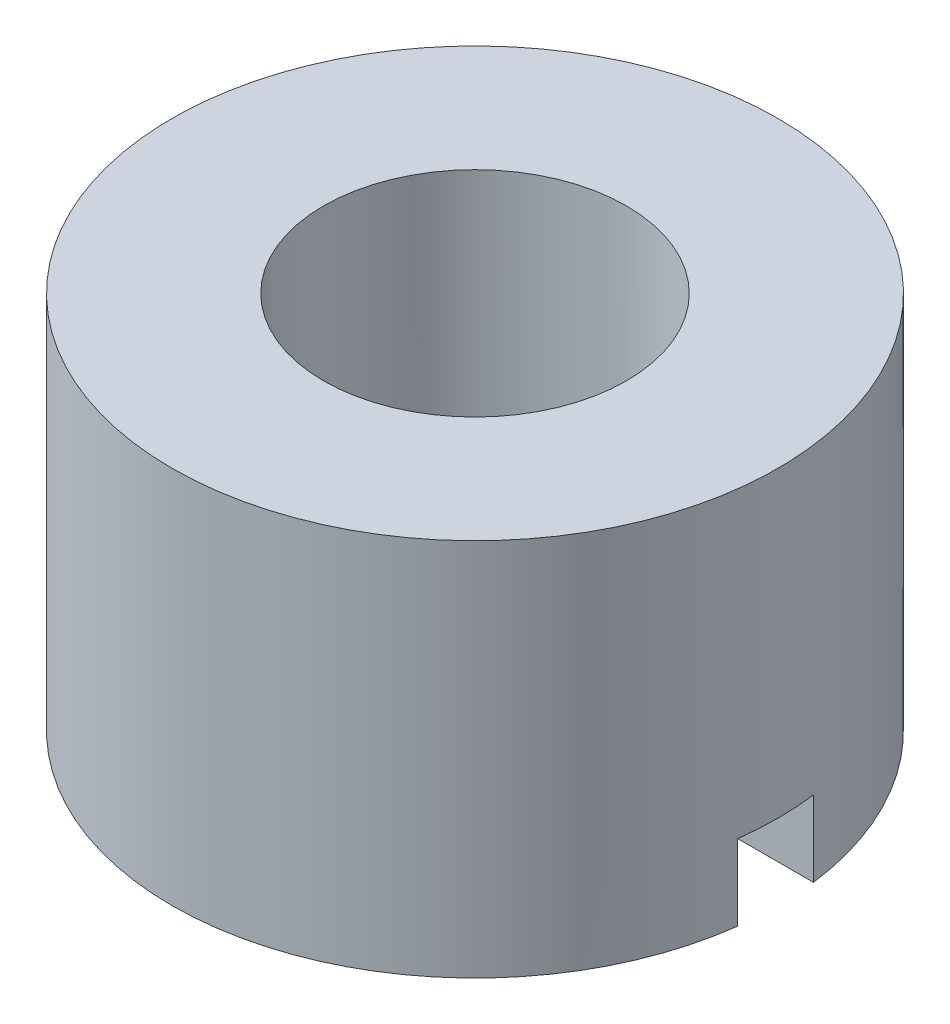
SolidWorks part; units mm, degrees
ref_plane "Front Plane" through (0, 0, 0) normal (0, 0, 1) x (1, 0, 0)
ref_plane "Top Plane" through (0, 0, 0) normal (0, 1, 0) x (1, 0, 0)
ref_plane "Right Plane" through (0, 0, 0) normal (1, 0, 0) x (0, 0, -1)
sketch "Sketch2" plane through (0, 0, 0) normal (1, 0, 0) x (0, 0, -1)
  line L0 (0, 8.0577) -> (0, -8.0577) construction
  line L1 (4, 4.8269) -> (4, -5.1731)
  line L2 (4, -5.1731) -> (8, -5.1731)
  line L3 (8, -5.1731) -> (8, 4.8269)
  line L4 (8, 4.8269) -> (4, 4.8269)
  dimension "D1" = 4
  dimension "D2" = 10
  dimension "D3" = 4
revolve "Revolve1" add sketch "Sketch2" angle 360 about L0
sketch "Sketch3" plane through (0, 0, 0) normal (1, 0, 0) x (0, 0, -1)
  line L0 (-8, -5.1731) -> (8, -5.1731) construction
  line L1 (-1, -3.1731) -> (1, -3.1731)
  line L2 (-1, -3.1731) -> (-1, -5.1731)
  line L3 (-1, -5.1731) -> (1, -5.1731)
  line L4 (1, -3.1731) -> (1, -5.1731)
  line L5 (-1, -3.1731) -> (1, -5.1731) construction
  line L6 (-1, -5.1731) -> (1, -3.1731) construction
  line L7 (0, 0) -> (0, -4.1731) construction
  point P0 (0, -4.1731)
  dimension "D1" = 2
  dimension "D2" = 2
extrude "Cut-Extrude1" cut sketch "Sketch3" against normal through all both and the other way through all
